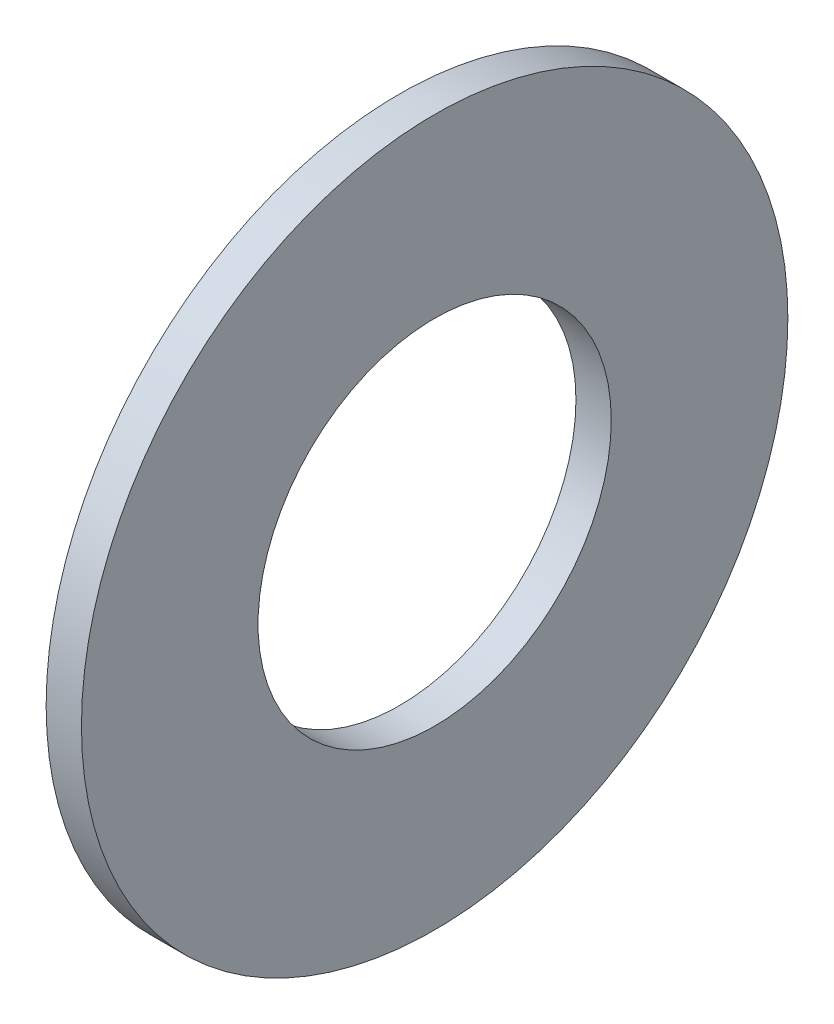
SolidWorks part; units mm, degrees
ref_plane "Front Plane" through (0, 0, 0) normal (0, 0, 1) x (1, 0, 0)
ref_plane "Top Plane" through (0, 0, 0) normal (0, 1, 0) x (1, 0, 0)
ref_plane "Right Plane" through (0, 0, 0) normal (1, 0, 0) x (0, 0, -1)
sketch "Sketch1" plane through (0, 0, 0) normal (1, 0, 0) x (0, 0, -1)
  circle A0 centre (0, 0) radius 20
  circle A1 centre (0, 0) radius 10
  dimension "D1" = 40
  dimension "D2" = 20
extrude "Boss-Extrude1" add sketch "Sketch1" along normal blind 2
